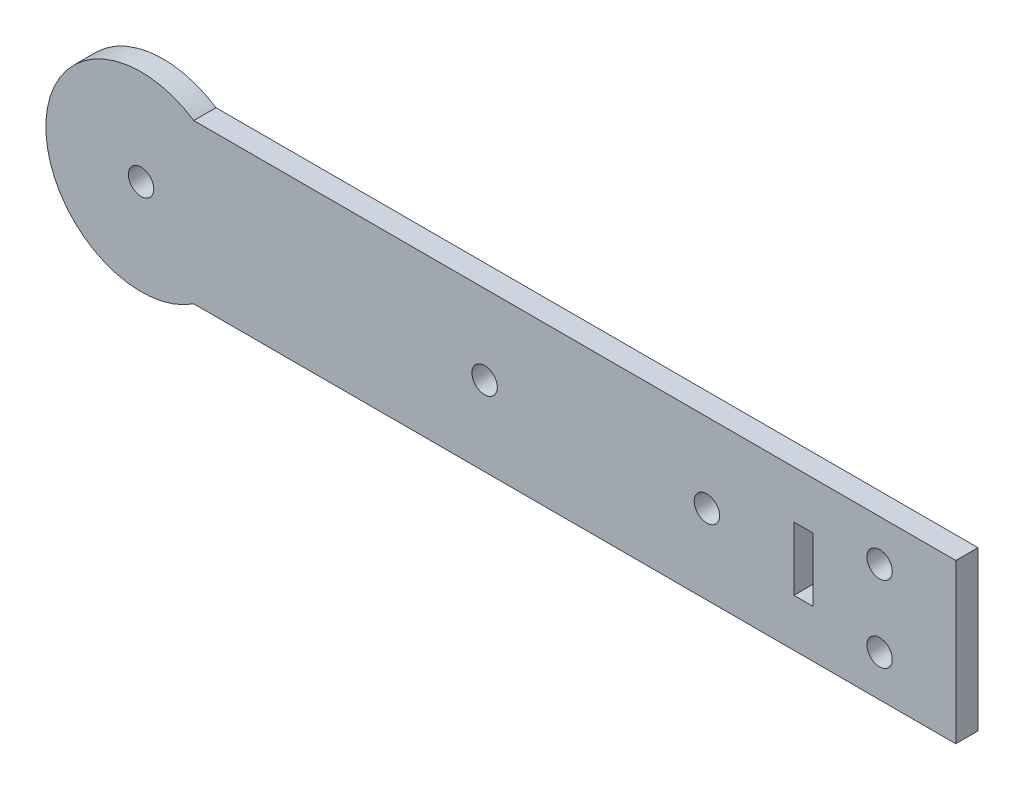
SolidWorks part; units mm, degrees
material "Balsa"
ref_plane "Alzado" through (0, 0, 0) normal (0, 0, 1) x (1, 0, 0)
ref_plane "Planta" through (0, 0, 0) normal (0, 1, 0) x (1, 0, 0)
ref_plane "Vista lateral" through (0, 0, 0) normal (1, 0, 0) x (0, 0, -1)
sketch "Croquis1" plane through (0, 0, 0) normal (0, 0, 1) x (1, 0, 0)
  line L0 (34.9022, 12.5) -> (34.9022, -12.5)
  line L5 (-85.0978, 12.5) -> (34.9022, 12.5)
  line L7 (-85.0978, -12.5) -> (34.9022, -12.5)
  line L8 (0, 0) -> (-8.8431, 0) construction
  line L10 (9.4022, 5) -> (12.4022, 5)
  line L11 (9.4022, 5) -> (9.4022, -5)
  line L12 (9.4022, -5) -> (12.4022, -5)
  line L13 (12.4022, 5) -> (12.4022, -5)
  line L14 (9.4022, 5) -> (12.4022, -5) construction
  line L15 (9.4022, -5) -> (12.4022, 5) construction
  arc A13 (-85.0978, 12.5) -> (-85.0978, -12.5) centre (-93.3894, 0) ccw
  circle A15 centre (-93.3894, 0) radius 2
  circle A17 centre (22.9022, 6) radius 2
  circle A18 centre (22.9022, -6) radius 2
  circle A19 centre (-39.2916, 0) radius 2
  circle A20 centre (-4.2916, 0) radius 2
  point P0 (0, 0)
  point P8 (10.9022, 0)
  dimension "D2" = 25
  dimension "D3" = 30
  dimension "D4" = 4
  dimension "D5" = 3
  dimension "D9" = 12
  dimension "D10" = 4
  dimension "D8" = 4
  dimension "D1" = 120
  dimension "D6" = 12.5
  dimension "D7" = 12
  dimension "D11" = 10
  dimension "D12" = 35
  dimension "D13" = 12.5
  dimension "D14" = 24
  dimension "D15" = 12.5
extrude "Saliente-Extruir2" add sketch "Croquis1" along normal blind 3.5
